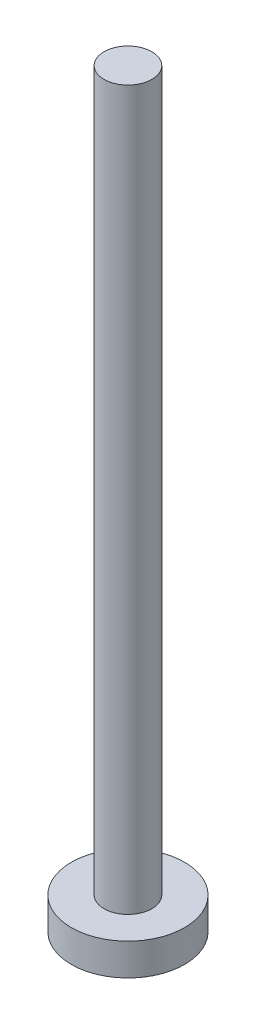
SolidWorks part; units mm, degrees
ref_plane "前视基准面" through (0, 0, 0) normal (0, 0, 1) x (1, 0, 0)
ref_plane "上视基准面" through (0, 0, 0) normal (0, 1, 0) x (1, 0, 0)
ref_plane "右视基准面" through (0, 0, 0) normal (1, 0, 0) x (0, 0, -1)
sketch "草图1" plane through (0, 0, 0) normal (0, 1, 0) x (1, 0, 0)
  circle A0 centre (0, 0) radius 3.55
  dimension "D1" = 7.1
extrude "凸台-拉伸1" add sketch "草图1" along normal blind 2
sketch "草图2" plane through (0, 2, 0) normal (0, 1, 0) x (1, 0, 0)
  circle A0 centre (0, 0) radius 1.5
  dimension "D1" = 3
extrude "凸台-拉伸2" add sketch "草图2" along normal blind 45
